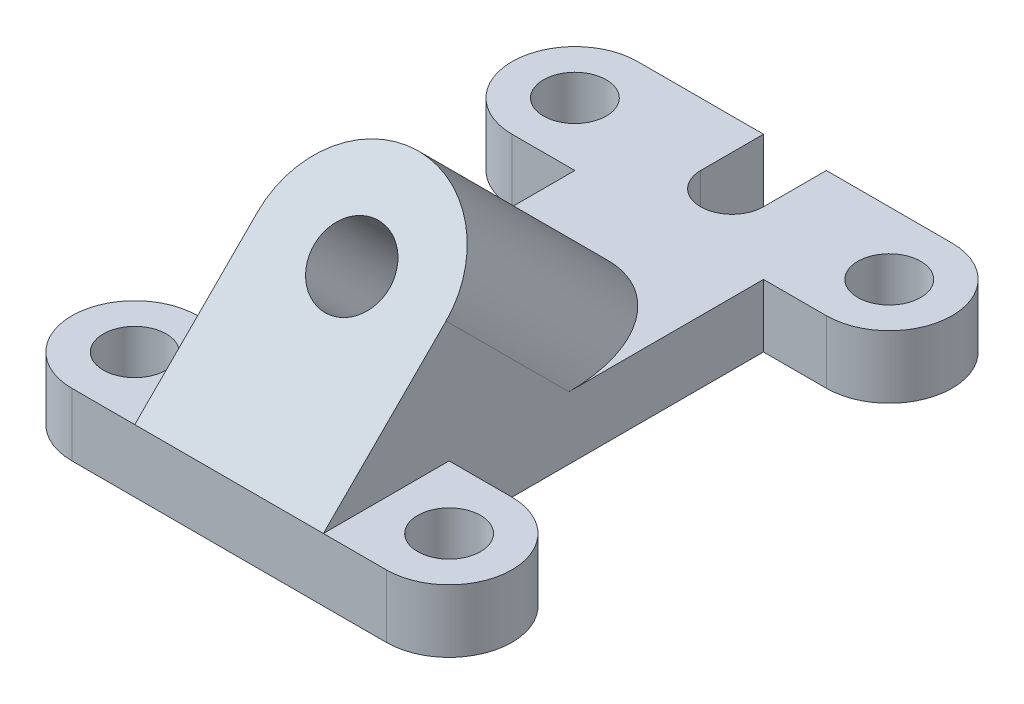
SolidWorks part; units mm, degrees
material "1060 Alloy"
ref_plane "Front Plane" through (0, 0, 0) normal (0, 0, 1) x (1, 0, 0)
ref_plane "Top Plane" through (0, 0, 0) normal (0, 1, 0) x (1, 0, 0)
ref_plane "Right Plane" through (0, 0, 0) normal (1, 0, 0) x (0, 0, -1)
sketch "Sketch2" plane through (0, 0, 0) normal (0, 1, 0) x (1, 0, 0)
  line L0 (-63.5, 101.6) -> (-38.1, 101.6)
  line L1 (-63.5, -12.7) -> (0, -12.7)
  line L2 (-63.5, 76.2) -> (-50.8, 76.2)
  line L3 (0, 76.2) -> (-12.7, 76.2)
  line L4 (-50.8, 76.2) -> (-50.8, 12.7)
  line L5 (-50.8, 12.7) -> (-63.5, 12.7)
  line L6 (-12.7, 76.2) -> (-12.7, 12.7)
  line L7 (-12.7, 12.7) -> (0, 12.7)
  line L8 (-38.1, 101.6) -> (-38.1, 88.9)
  line L9 (-25.4, 88.9) -> (-25.4, 101.6)
  line L10 (-25.4, 101.6) -> (0, 101.6)
  circle A0 centre (0, 0) radius 6.35
  circle A1 centre (0, 88.9) radius 6.35
  circle A2 centre (-63.5, 0) radius 6.35
  circle A3 centre (-63.5, 88.9) radius 6.35
  arc A4 (-63.5, 101.6) -> (-63.5, 76.2) centre (-63.5, 88.9) ccw
  arc A5 (0, 76.2) -> (0, 101.6) centre (0, 88.9) ccw
  arc A6 (-63.5, 12.7) -> (-63.5, -12.7) centre (-63.5, 0) ccw
  arc A7 (0, -12.7) -> (0, 12.7) centre (0, 0) ccw
  arc A8 (-38.1, 88.9) -> (-25.4, 88.9) centre (-31.75, 88.9) ccw
  dimension "D2" = 12.7
  dimension "D4" = 12.7
  dimension "D1" = 63.5
  dimension "D3" = 88.9
  dimension "D5" = 38.1
  dimension "D6" = 12.7
  dimension "D7" = 25.4
  dimension "D8" = 12.7
  dimension "D9" = 12.7
extrude "Boss-Extrude1" add sketch "Sketch2" along normal blind 12.7
ref_plane "Plane1" through (0, 12.7, 12.7) normal (0, 0.7071, 0.7071) x (1, 0, 0)
sketch "Sketch4" plane through (0, 12.7, 12.7) normal (0, 0.7071, 0.7071) x (1, 0, 0)
  line L0 (-50.8, 0) -> (-50.8, 35.052)
  line L1 (-63.5, 0) -> (0, 0) construction
  line L2 (-50.8, 62.8618) -> (-50.8, 17.9605) construction
  line L3 (-12.7, 17.9605) -> (-12.7, 62.8618) construction
  line L4 (-12.7, 35.052) -> (-12.7, 0)
  line L5 (-50.8, 0) -> (-12.7, 0)
  arc A0 (-50.8, 35.052) -> (-12.7, 35.052) centre (-31.75, 35.052) cw
  circle A1 centre (-31.75, 35.052) radius 7.62
  dimension "D2" = 15.24
  dimension "D1" = 35.052
extrude "Boss-Extrude2" add sketch "Sketch4" against normal up to next
